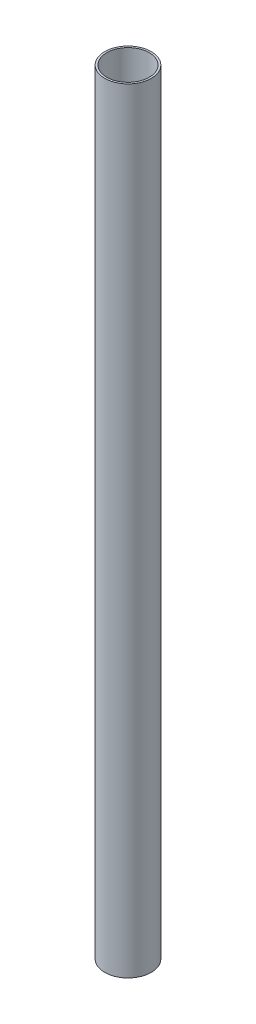
SolidWorks part; units mm, degrees
material "Vidro"
ref_plane "Plano frontal" through (0, 0, 0) normal (0, 0, 1) x (1, 0, 0)
ref_plane "Plano superior" through (0, 0, 0) normal (0, 1, 0) x (1, 0, 0)
ref_plane "Plano direito" through (0, 0, 0) normal (1, 0, 0) x (0, 0, -1)
sketch "Esboço1" plane through (0, 0, 0) normal (0, 1, 0) x (1, 0, 0)
  circle A0 centre (0, 0) radius 27.5
  circle A1 centre (0, 0) radius 30
  dimension "D1" = 55
  dimension "D2" = 60
extrude "Ressalto-extrusão1" add sketch "Esboço1" along normal blind 940 and the other way blind 60
